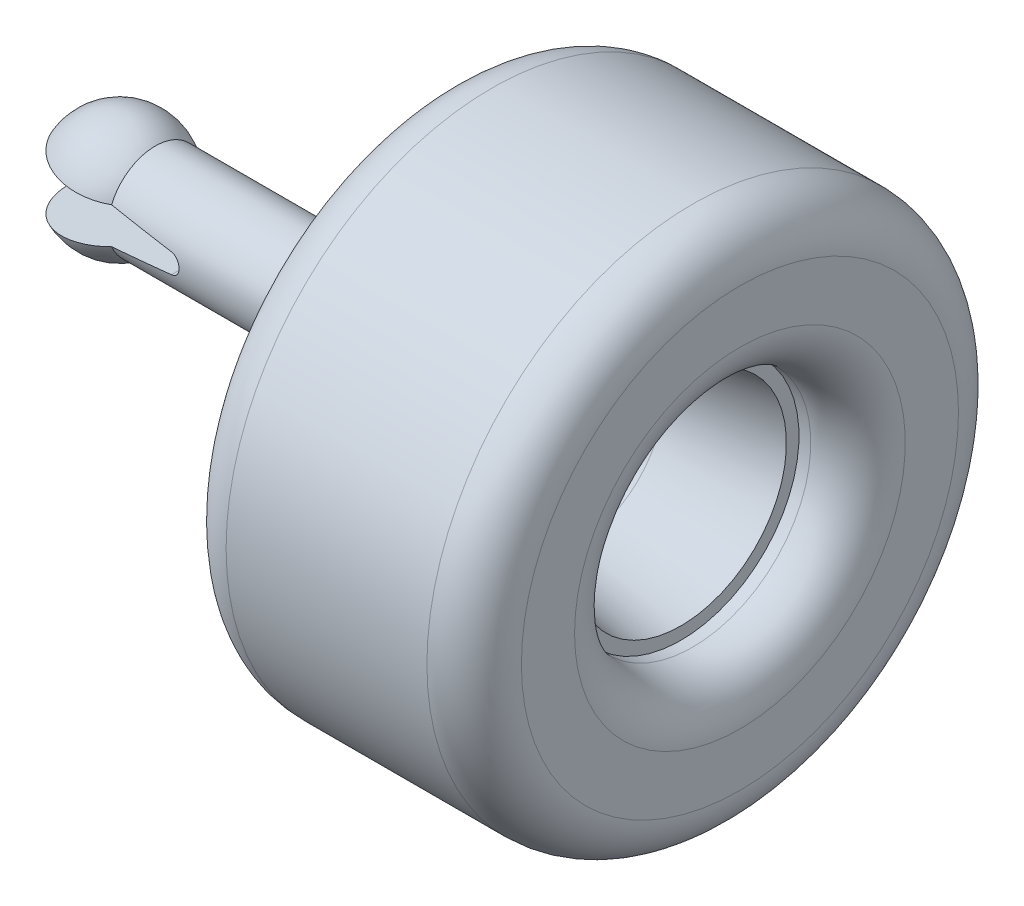
SolidWorks part; units mm, degrees
ref_plane "前基準面" through (0, 0, 0) normal (0, 0, 1) x (1, 0, 0)
ref_plane "上基準面" through (0, 0, 0) normal (0, 1, 0) x (1, 0, 0)
ref_plane "右基準面" through (0, 0, 0) normal (1, 0, 0) x (0, 0, -1)
sketch "草圖1" plane through (0, 0, 0) normal (0, 0, 1) x (1, 0, 0)
  line L0 (0, 0) -> (105, 0) construction
  line L1 (6, 8) -> (49, 8)
  line L2 (55, 14) -> (55, 37)
  line L3 (63, 45) -> (97, 45)
  line L4 (105, 37) -> (105, 28)
  line L5 (95, 20) -> (97, 20)
  line L6 (95, 20) -> (95, 17.8763)
  line L7 (66.1557, 5.7738) -> (75, 5)
  line L8 (75, 5) -> (75, 0)
  line L9 (77.3953, 14.7721) -> (95, 17.8763)
  line L10 (-10, 0) -> (75, 0)
  arc A0 (6, 8) -> (-10, 0) centre (0, 0) ccw
  arc A1 (49, 8) -> (55, 14) centre (49, 14) ccw
  arc A2 (55, 37) -> (63, 45) centre (63, 37) cw
  arc A3 (105, 28) -> (97, 20) centre (97, 28) cw
  arc A4 (105, 37) -> (97, 45) centre (97, 37) ccw
  arc A5 (77.3953, 14.7721) -> (66.1557, 5.7738) centre (80, 0) ccw
  point P4 (0, 0)
  point P25 (0, 0)
  dimension "D2" = 10
  dimension "D4" = 6
  dimension "D5" = 8
  dimension "D6" = 8
  dimension "D13" = 15
  dimension "D16" = 105
  dimension "D3" = 16
  dimension "D7" = 90
  dimension "D8" = 40
  dimension "D9" = 50
  dimension "D10" = 5
  dimension "D11" = 5
  dimension "D12" = 10
  dimension "D14" = 10
  dimension "D15" = 20
  dimension "D17" = 25
revolve "旋轉1" add sketch "草圖1" angle 360 about L0
sketch "草圖2" plane through (0, 0, 0) normal (0, 0, 1) x (1, 0, 0)
  line L0 (-8.6603, 5) -> (16.5609, 1.6796)
  line L1 (-10, 0) -> (75, 0) construction
  line L2 (-13.201, 0) -> (25.5444, 0) construction
  line L3 (-8.6603, -5) -> (16.5609, -1.6796)
  arc A0 (6, 8) -> (-10, 0) centre (0, 0) ccw construction
  arc A1 (16.5609, 1.6796) -> (16.5609, -1.6796) centre (16.3397, 0) cw
  dimension "D1" = 10
  dimension "D2" = 15
  dimension "D3" = 25
extrude "除料-伸長1" cut sketch "草圖2" against normal through all and the other way through all
